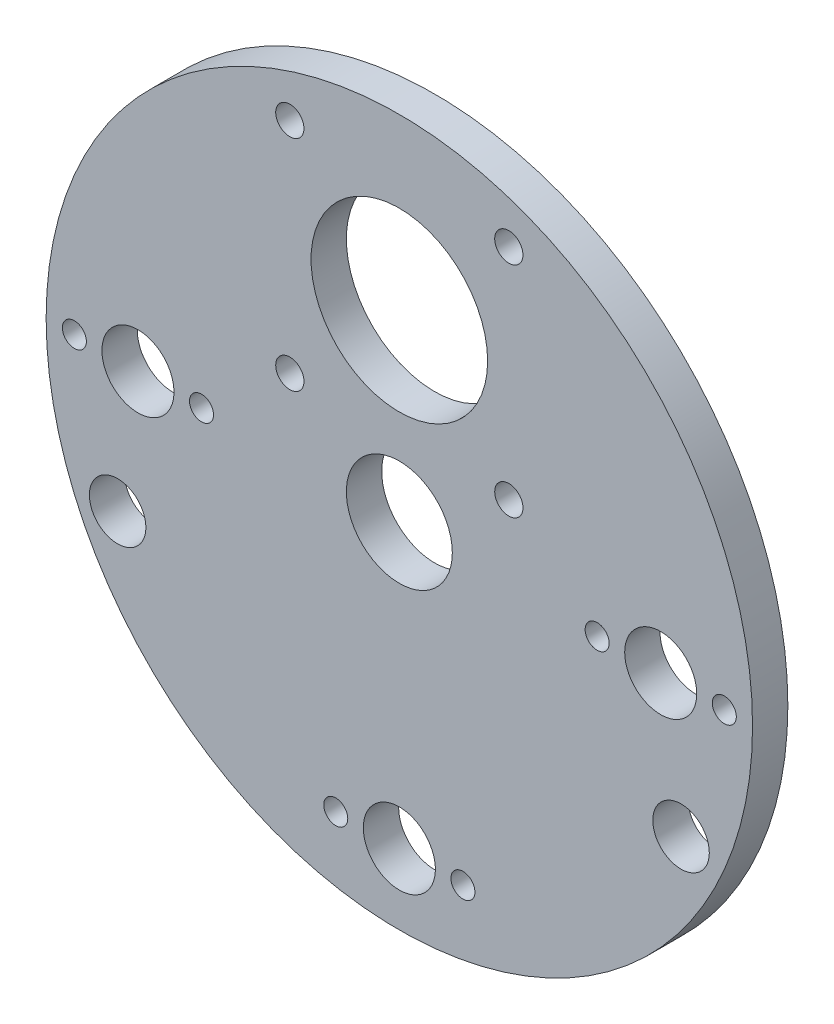
SolidWorks part; units mm, degrees
material "Acrylic (Medium-high impact)"
ref_plane "Front Plane" through (0, 0, 0) normal (0, 0, 1) x (1, 0, 0)
ref_plane "Top Plane" through (0, 0, 0) normal (0, 1, 0) x (1, 0, 0)
ref_plane "Right Plane" through (0, 0, 0) normal (1, 0, 0) x (0, 0, -1)
sketch "Sketch1" plane through (0, 0, 0) normal (0, 0, 1) x (1, 0, 0)
  circle A0 centre (0, 0) radius 50
  dimension "D1" = 100
extrude "Boss-Extrude1" add sketch "Sketch1" along normal blind 5
hole_wizard "Ø10.2 (10.2) Diameter Hole1" positions "Sketch5" profile "Sketch6" hole size "Ø10.2" standard "ISO"
sketch "Sketch5" plane through (0, 0, 0) normal (0, 0, -1) x (-1, 0, 0)
  point P4 (37, 0)
  point P17 (-37, 0)
  point P21 (0, -37) [skipped]
  point P23 (0, -40)
  dimension "D1" = 3
  dimension "D3" = 37
sketch "Sketch6" plane through (-37, 0, 0) normal (1, 0, 0) x (0, 1, 0)
  line L0 (0, 0) -> (0, 5)
  line L1 (0, 5) -> (5.1, 5)
  line L2 (5.1, 5) -> (5.1, 0)
  line L5 (5.1, 0) -> (0, 0)
  line L11 (0, -6.35) -> (0, 107.95) construction
  dimension "Thru Hole Dia." = 10.2
  dimension "Thru Hole Depth" = 5
hole_wizard "M3 Clearance Hole1" positions "Sketch7" profile "Sketch8" hole size "M3" standard "ISO" end condition through all
sketch "Sketch7" plane through (0, 0, 5) normal (0, 0, 1) x (1, 0, 0)
  circle A0 centre (37, 0) radius 5.1 construction
  circle A1 centre (0, -40) radius 5.1 construction
  point P0 (46, 0)
  point P2 (28, 0)
  point P11 (9, -40)
  point P13 (-9, -40)
  point P46 (-46, 0)
  point P47 (-28, 0)
  dimension "D2" = 9
  dimension "D1" = 9
  dimension "D4" = 9
  dimension "D5" = 9
  dimension "D6" = 2
  dimension "D3" = 40
sketch "Sketch8" plane through (46, 0, 5) normal (1, 0, 0) x (0, -1, 0)
  line L0 (0, 0) -> (0, 5)
  line L1 (0, 5) -> (1.7, 5)
  line L2 (1.7, 5) -> (1.7, 0)
  line L5 (1.7, 0) -> (0, 0)
  line L11 (0, -6.35) -> (0, 107.95) construction
  dimension "Thru Hole Dia." = 3.4
  dimension "Thru Hole Depth" = 5
sketch "Sketch12" plane through (0, 0, 5) normal (0, 0, 1) x (1, 0, 0)
  circle A0 centre (0, 26) radius 12.5
  dimension "D1" = 25
  dimension "D2" = 26
extrude "Cut-Extrude2" cut sketch "Sketch12" against normal blind 10 contours A0
sketch "Sketch13" plane through (0, 0, 5) normal (0, 0, 1) x (1, 0, 0)
  circle A0 centre (-15.5, 41.5) radius 2
  circle A1 centre (0, 26) radius 12.5 construction
  dimension "D1" = 15.5
  dimension "D2" = 15.5
  dimension "D3" = 4
extrude "Cut-Extrude3" cut sketch "Sketch13" against normal blind 10
pattern_circular "CirPattern1" count 4 over 360 about axis through (0, 26, 0) along (0, 0, 1) of "Cut-Extrude3"
sketch "Sketch14" plane through (0, 0, 5) normal (0, 0, 1) x (1, 0, 0)
  line L0 (0, 0) -> (-39.8775, -18.5952) construction
  line L1 (0, 0) -> (0, -25.0581) construction
  circle A0 centre (-39.8775, -18.5952) radius 4
  circle A1 centre (39.8775, -18.5952) radius 4
  dimension "D1" = 8
  dimension "D2" = 44
  dimension "D3" = 65
extrude "Cut-Extrude4" cut sketch "Sketch14" against normal blind 10
sketch "Sketch15" plane through (0, 0, 5) normal (0, 0, 1) x (1, 0, 0)
  circle A0 centre (0, 0) radius 7.5
  dimension "D1" = 15
extrude "Cut-Extrude5" cut sketch "Sketch15" against normal blind 10
